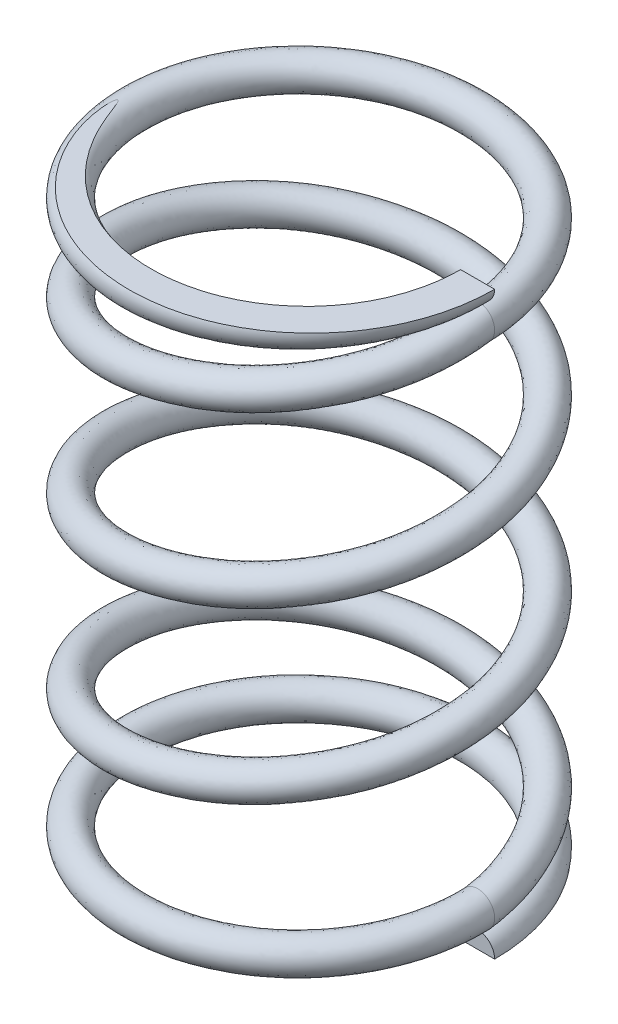
SolidWorks part; units mm, degrees
ref_plane "Front" through (0, 0, 0) normal (0, 0, 1) x (1, 0, 0)
ref_plane "Top" through (0, 0, 0) normal (0, 1, 0) x (1, 0, 0)
ref_plane "Right" through (0, 0, 0) normal (1, 0, 0) x (0, 0, -1)
sketch "Sketch1" plane through (0, 0, 0) normal (0, 0, 1) x (1, 0, 0)
  line L0 (2.7686, 9.525) -> (2.7686, 9.2456) construction
  line L1 (0, 0) -> (2.7686, 0) construction
  line L2 (0, 0) -> (0, 9.525) construction
  line L3 (0, 9.525) -> (2.7686, 9.525) construction
  line L4 (2.7686, 9.2456) -> (2.7686, 9.2202) construction
  line L5 (2.7686, 9.2202) -> (2.7686, 8.6614) construction
  line L6 (2.7686, 8.6614) -> (2.7686, 0.8636) construction
  line L7 (2.7686, 0.8636) -> (2.7686, 0.3048) construction
  line L8 (2.7686, 0.3048) -> (2.7686, 0.2794) construction
  line L9 (2.7686, 0.2794) -> (2.7686, 0) construction
  line L10 (2.7686, 0) -> (3.048, 0) construction
  line L11 (2.7686, 0.5842) -> (3.048, 0.5842) construction
  line L12 (2.7686, 9.525) -> (3.048, 9.525) construction
  line L13 (2.7686, 9.525) -> (2.7686, 9.8044) construction
  line L14 (2.7686, 0) -> (2.7686, -0.2794) construction
  circle A0 centre (2.7686, 9.525) radius 0.2794 construction
  circle A1 centre (2.7686, 8.9408) radius 0.2794 construction
  circle A2 centre (2.7686, 0.5842) radius 0.2794
  circle A3 centre (2.7686, 0) radius 0.2794 construction
  dimension "Wire Dia" = 0.5588
  dimension "D3" = 8.3566
  dimension "D4" = 0.5842
  dimension "D1" = 0.0254
  dimension "Spring-OD" = 6.096
  dimension "Overall Height" = 9.525
ref_plane "Plane1" through (0, 0.5842, 0) normal (0, 1, 0) x (-1, 0, 0)
sketch "Sketch3" plane through (0, 0.5842, 0) normal (0, 1, 0) x (-1, 0, 0)
  circle A0 centre (0, 0) radius 3.048
curve "Helix1" pitch 2.7855 height 8.3566 turns 3
sweep "Sweep1" add profiles "Sketch1" path "Helix1"
sketch "Sketch4" plane through (0, 0.5842, 0) normal (0, 1, 0) x (-1, 0, 0)
  circle A0 centre (0, 0) radius 3.048 construction
  circle A1 centre (0, 0) radius 3.048
curve "Helix2" pitch 0.5842 height 0.5842 turns 1
sketch "Sketch5" plane through (0, 0, 0) normal (0, 0, 1) x (1, 0, 0)
  circle A0 centre (2.7686, 0) radius 0.2794 construction
  circle A1 centre (2.7686, 0) radius 0.2794
sweep "Sweep2" add profiles "Sketch5" path "Helix2"
ref_plane "Plane2" through (0, 8.9408, 0) normal (0, 1, 0) x (-1, 0, 0)
sketch "Sketch6" plane through (0, 8.9408, 0) normal (0, 1, 0) x (-1, 0, 0)
  circle A0 centre (0, 0) radius 3.048 construction
  circle A1 centre (0, 0) radius 3.048
curve "Helix3" pitch 0.5842 height 0.5842 turns 1
sketch "Sketch7" plane through (0, 0, 0) normal (0, 0, 1) x (1, 0, 0)
  circle A0 centre (2.7686, 8.9408) radius 0.2794 construction
  circle A1 centre (2.7686, 8.9408) radius 0.2794
sweep "Sweep3" add profiles "Sketch7" path "Helix3"
sketch "Sketch8" plane through (0, 0, 0) normal (0, 0, 1) x (1, 0, 0)
  line L0 (0, 0) -> (0, 9.525) construction
  line L1 (0, 9.525) -> (3.048, 9.525)
  line L2 (0, 9.525) -> (0, 9.8044)
  line L3 (0, 9.8044) -> (3.048, 9.8044)
  line L4 (3.048, 9.525) -> (3.048, 9.8044)
  line L5 (0, 0) -> (3.048, 0)
  line L6 (0, 0) -> (0, -0.2794)
  line L7 (0, -0.2794) -> (3.048, -0.2794)
  line L8 (3.048, 0) -> (3.048, -0.2794)
  line L9 (0, 0) -> (0, 9.525) construction
revolve "Cut-Revolve1" cut sketch "Sketch8" angle 360 about L9
equation "\"D3@Helix1\"=\"D3@Sketch1\""
equation "\"D3@Helix2\"=\"D4@Sketch1\""
equation "\"D3@Helix3\"=\"D4@Sketch1\""
